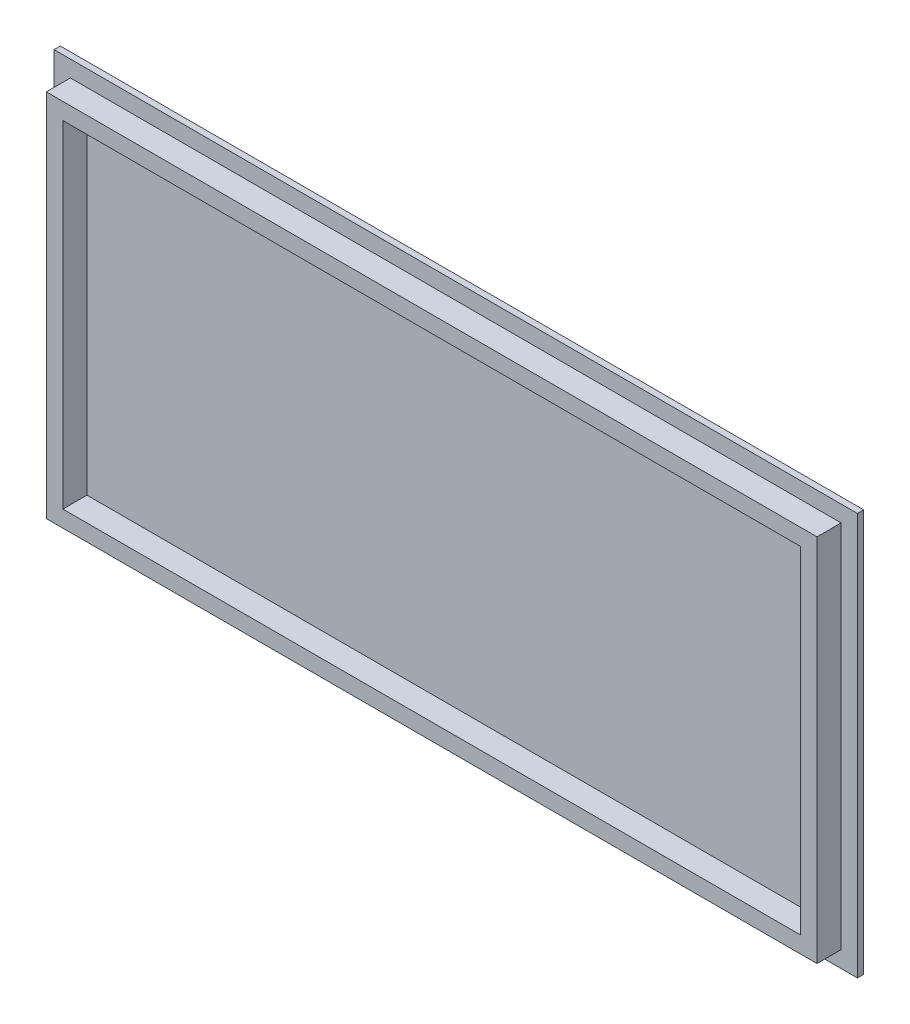
SolidWorks part; units mm, degrees
ref_plane "Front Plane" through (0, 0, 0) normal (0, 0, 1) x (1, 0, 0)
ref_plane "Top Plane" through (0, 0, 0) normal (0, 1, 0) x (1, 0, 0)
ref_plane "Right Plane" through (0, 0, 0) normal (1, 0, 0) x (0, 0, -1)
sketch "Model" plane through (0, 0, 0) normal (0, 0, 1) x (1, 0, 0)
  line L0 (189.071, 8.2737) -> (131.917, 8.2737)
  line L1 (-7.9049, -7.7268) -> (-7.9354, 184.294)
  line L2 (-7.9354, 184.294) -> (375.4737, 184.294)
  line L3 (375.4737, 184.294) -> (375.566, -7.7437)
  line L4 (375.566, -7.7437) -> (-7.9049, -7.7268)
  line L5 (-0.1101, 0.0729) -> (-0.1014, 176.494)
  line L6 (7.7946, 7.9723) -> (7.7873, 168.593)
  line L7 (-0.1014, 176.494) -> (367.7633, 176.494)
  line L8 (7.7873, 168.593) -> (359.8705, 168.593)
  line L9 (359.8705, 168.593) -> (359.8675, 7.9723)
  line L10 (367.7633, 176.494) -> (367.766, 0.0792)
  line L11 (359.8675, 7.9723) -> (7.7946, 7.9723)
  line L12 (367.766, 0.0792) -> (-0.1101, 0.0729)
sketch "草图5" plane through (0, 0, 0) normal (0, 0, 1) x (1, 0, 0)
  line L5 (-7.9354, 184.294) -> (375.566, -7.7437) construction
  line L7 (375.5503, -7.7448) -> (-7.9197, -7.7448)
  line L8 (375.5503, -7.7448) -> (375.5503, 184.2952)
  line L9 (375.5503, 184.2952) -> (-7.9197, 184.2952)
  line L10 (-7.9197, -7.7448) -> (-7.9197, 184.2952)
  line L11 (375.5503, -7.7448) -> (-7.9197, 184.2952) construction
  line L12 (375.5503, 184.2952) -> (-7.9197, -7.7448) construction
  point P2 (183.8153, 88.2752)
  dimension "D1" = 383.47
  dimension "D2" = 192.04
extrude "凸台-拉伸2" add sketch "草图5" along normal blind 3
sketch "草图6" plane through (0, 0, 0) normal (0, 0, 1) x (1, 0, 0)
  line L0 (-0.1014, 176.494) -> (367.766, 0.0792) construction
  line L1 (359.8675, 7.9723) -> (7.7873, 168.593) construction
  line L3 (367.7723, 0.0816) -> (-0.1077, 0.0816)
  line L4 (367.7723, 0.0816) -> (367.7723, 176.4916)
  line L5 (367.7723, 176.4916) -> (-0.1077, 176.4916)
  line L6 (-0.1077, 0.0816) -> (-0.1077, 176.4916)
  line L7 (367.7723, 0.0816) -> (-0.1077, 176.4916) construction
  line L8 (367.7723, 176.4916) -> (-0.1077, 0.0816) construction
  point P8 (183.8323, 88.2866)
  dimension "D1" = 367.88
  dimension "D2" = 176.41
extrude "凸台-拉伸3" add sketch "草图6" along normal blind 11.5 from surface at 3 starting at face at (183.8153, 88.2752, 3)
sketch "草图7" plane through (0, 0, 0) normal (0, 0, 1) x (1, 0, 0)
  line L0 (359.8675, 7.9723) -> (7.7873, 168.593) construction
  line L2 (7.7924, 7.9726) -> (359.8624, 7.9726)
  line L3 (7.7924, 7.9726) -> (7.7924, 168.5926)
  line L4 (7.7924, 168.5926) -> (359.8624, 168.5926)
  line L5 (359.8624, 7.9726) -> (359.8624, 168.5926)
  line L6 (7.7924, 7.9726) -> (359.8624, 168.5926) construction
  line L7 (7.7924, 168.5926) -> (359.8624, 7.9726) construction
  point P4 (183.8274, 88.2826)
  dimension "D1" = 352.07
  dimension "D2" = 160.62
extrude "切除-拉伸1" cut sketch "草图7" against normal blind 11.5 from surface at 14.5 starting at face at (183.8323, 88.2866, 14.5)
